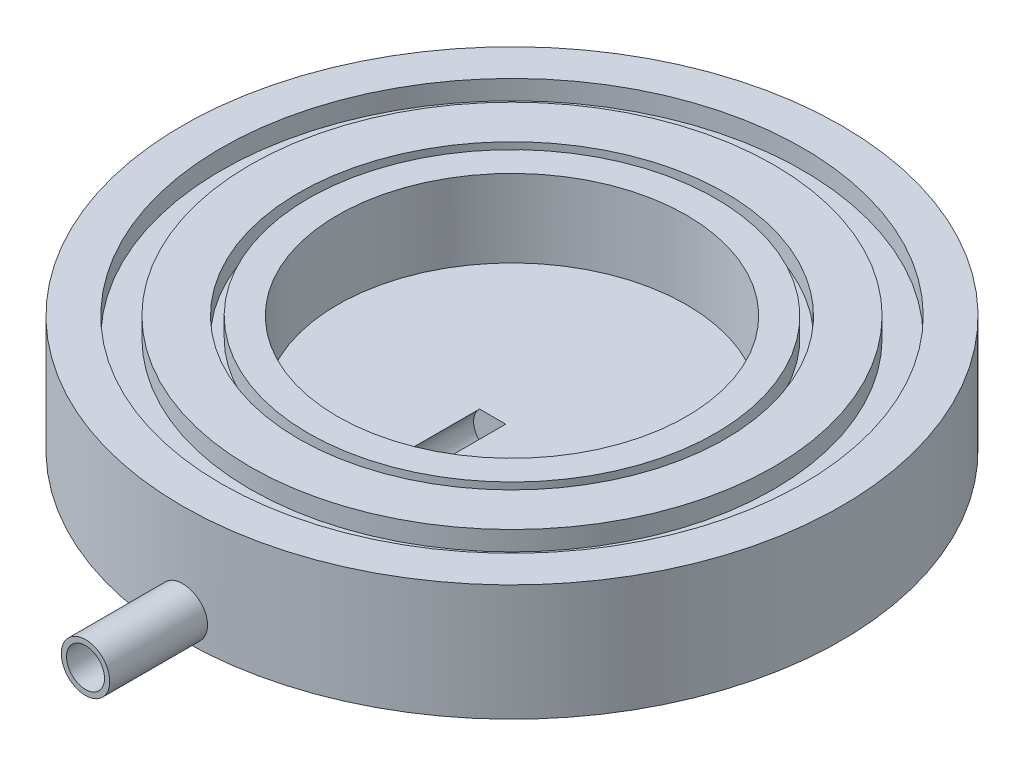
SolidWorks part; units mm, degrees
ref_plane "Front Plane" through (0, 0, 0) normal (0, 0, 1) x (1, 0, 0)
ref_plane "Top Plane" through (0, 0, 0) normal (0, 1, 0) x (1, 0, 0)
ref_plane "Right Plane" through (0, 0, 0) normal (1, 0, 0) x (0, 0, -1)
sketch "Sketch1" plane through (0, 0, 0) normal (0, 1, 0) x (1, 0, 0)
  circle A0 centre (0, 0) radius 17
  dimension "D1" = 34
extrude "Boss-Extrude1" add sketch "Sketch1" along normal blind 6
sketch "Sketch2" plane through (0, 6, 0) normal (0, 1, 0) x (1, 0, 0)
  circle A0 centre (0, 0) radius 15
  circle A1 centre (0, 0) radius 13.5
  dimension "D1" = 27
  dimension "30" = 30
extrude "Cut-Extrude1" cut sketch "Sketch2" against normal blind 1
sketch "Sketch3" plane through (0, 6, 0) normal (0, 1, 0) x (1, 0, 0)
  circle A0 centre (0, 0) radius 10.5
  circle A1 centre (0, 0) radius 11
  dimension "D1" = 22
  dimension "21" = 21
extrude "Cut-Extrude2" cut sketch "Sketch3" against normal blind 1
sketch "Sketch4" plane through (0, 6, 0) normal (0, 1, 0) x (1, 0, 0)
  circle A0 centre (0, 0) radius 9
  dimension "18" = 18
extrude "Cut-Extrude3" cut sketch "Sketch4" against normal blind 4
sketch "Sketch8" plane through (0, 0, 0) normal (0, 0, 1) x (1, 0, 0)
  circle A0 centre (0, 1.289) radius 1.25
  dimension "D1" = 2.5
extrude "Boss-Extrude2" add sketch "Sketch8" along normal blind 22
sketch "Sketch9" plane through (0, 6, 0) normal (0, 1, 0) x (1, 0, 0)
  circle A0 centre (0, 0) radius 9
extrude "Cut-Extrude5" cut sketch "Sketch9" against normal blind 4
sketch "Sketch10" plane through (0, 0, 22) normal (0, 0, 1) x (1, 0, 0)
  circle A0 centre (0, 1.289) radius 0.9813
extrude "Cut-Extrude6" cut sketch "Sketch10" against normal blind 21
